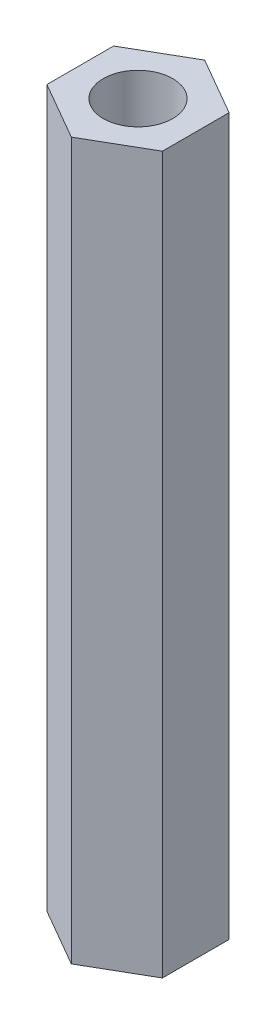
SolidWorks part; units mm, degrees
material "1023 Carbon Steel Sheet (SS)"
ref_plane "Front Plane" through (0, 0, 0) normal (0, 0, 1) x (1, 0, 0)
ref_plane "Top Plane" through (0, 0, 0) normal (0, 1, 0) x (1, 0, 0)
ref_plane "Right Plane" through (0, 0, 0) normal (1, 0, 0) x (0, 0, -1)
ref_plane "Top Plane1" through (0, 31, 0) normal (0, 1, 0) x (1, 0, 0)
sketch "Sketch1" plane through (0, 0, 0) normal (0, 1, 0) x (1, 0, 0)
  line L0 (0, 2.8868) -> (0, -2.8868) construction
  line L1 (2.5, 1.4434) -> (0, 2.8868)
  line L2 (0, 2.8868) -> (-2.5, 1.4434)
  line L3 (-2.5, 1.4434) -> (-2.5, -1.4434)
  line L4 (-2.5, -1.4434) -> (0, -2.8868)
  line L5 (0, -2.8868) -> (2.5, -1.4434)
  line L6 (2.5, -1.4434) -> (2.5, 1.4434)
  line L7 (0, -55) -> (0, 55) construction
  circle A0 centre (0, 0) radius 2.5 construction
  dimension "D1" = 5
extrude "Boss-Extrude1" add sketch "Sketch1" along normal blind 31
sketch "Sketch2" plane through (0, 0, 0) normal (0, 1, 0) x (1, 0, 0)
  circle A0 centre (0, 0) radius 1.5025
  dimension "D1" = 3.005
extrude "Cut-Extrude1" cut sketch "Sketch2" along normal blind 6.005
sketch "Sketch3" plane through (0, 31, 0) normal (0, 1, 0) x (1, 0, 0)
  circle A0 centre (0, 0) radius 1.5025
  dimension "D1" = 3.005
extrude "Cut-Extrude2" cut sketch "Sketch3" against normal blind 3.005
